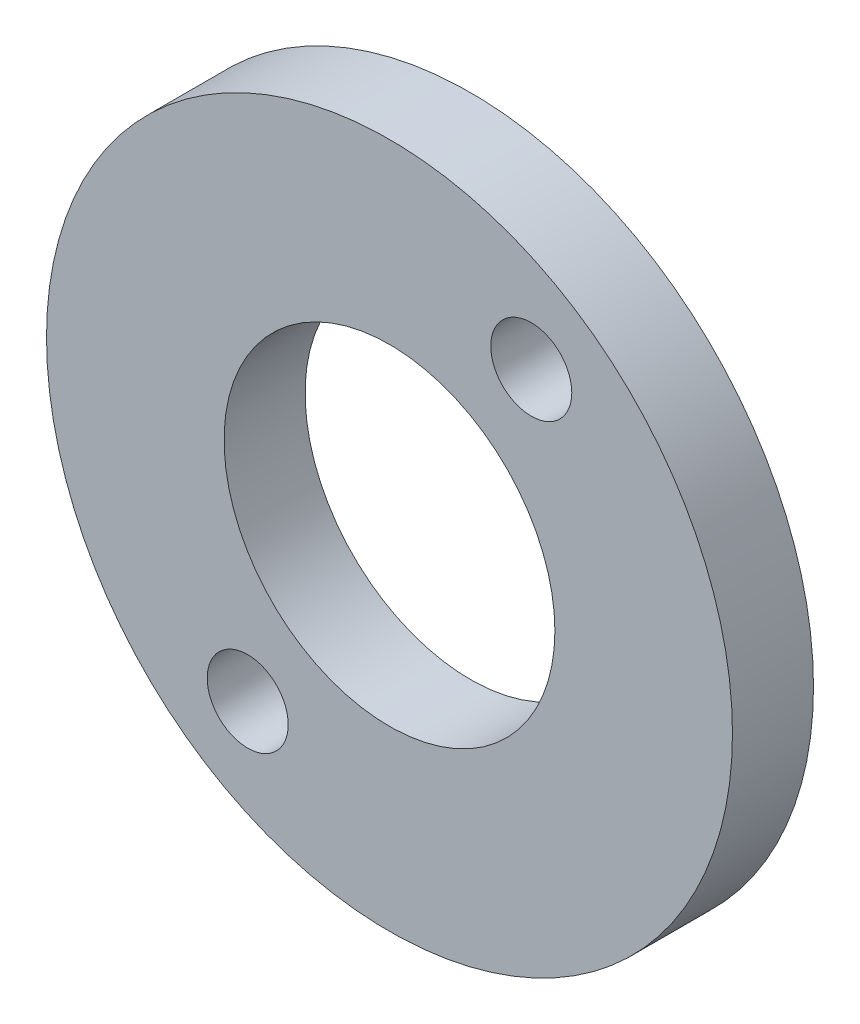
SolidWorks part; units mm, degrees
ref_plane "Front Plane" through (0, 0, 0) normal (0, 0, 1) x (1, 0, 0)
ref_plane "Top Plane" through (0, 0, 0) normal (0, 1, 0) x (1, 0, 0)
ref_plane "Right Plane" through (0, 0, 0) normal (1, 0, 0) x (0, 0, -1)
ref_plane "Plane1" through (0, 0, 129.2583) normal (0, 0, 1) x (1, 0, 0)
sketch "Sketch2" plane through (0, 0, 129.2583) normal (0, 0, 1) x (1, 0, 0)
  circle A0 centre (-25.9121, -505.1463) radius 6.125 construction
  circle A1 centre (-25.9121, -505.1463) radius 6.125
  circle A2 centre (-25.9121, -505.1463) radius 9.525 construction
  circle A3 centre (-31.1621, -513.0938) radius 1.5
  circle A4 centre (-20.6621, -497.1987) radius 1.5
  circle A5 centre (-25.9121, -505.1463) radius 12.7
  dimension "D4" = 19.05
  dimension "D1" = 3
  dimension "D7" = 25.4
  dimension "D3" = 5.25
  dimension "D5" = 5.25
  dimension "D6" = 9.525
  dimension "D2" = 2
extrude "Boss-Extrude1" add sketch "Sketch2" along normal blind 3
equation "\"D5@Sketch2\"=\"D3@Sketch2\""
